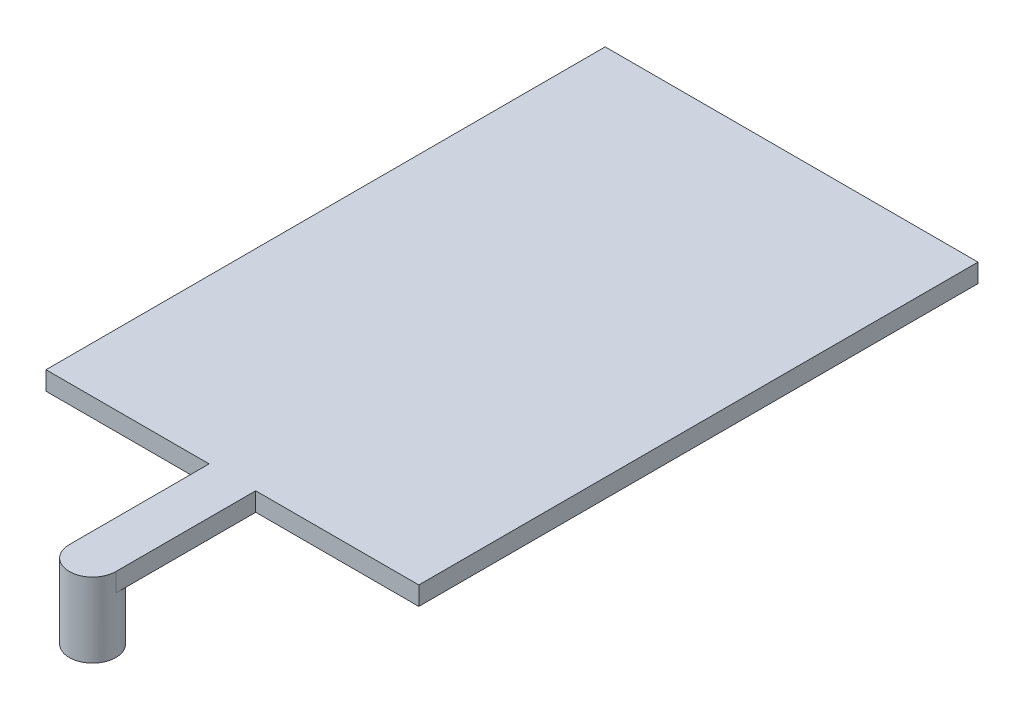
SolidWorks part; units mm, degrees
material "Медь"
ref_plane "Спереди" through (0, 0, 0) normal (0, 0, 1) x (1, 0, 0)
ref_plane "Сверху" through (0, 0, 0) normal (0, 1, 0) x (1, 0, 0)
ref_plane "Справа" through (0, 0, 0) normal (1, 0, 0) x (0, 0, -1)
sketch "Эскиз1" plane through (0, 0, 0) normal (0, 1, 0) x (1, 0, 0)
  line L0 (-0.125, -1.5) -> (0.125, -1.5)
  line L1 (-1, -1.5) -> (1, -1.5)
  line L2 (-1, -1.5) -> (-1, 1.5)
  line L3 (-1, 1.5) -> (1, 1.5)
  line L4 (1, -1.5) -> (1, 1.5)
  line L5 (-1, -1.5) -> (1, 1.5) construction
  line L6 (-1, 1.5) -> (1, -1.5) construction
  line L7 (-0.125, -1.5) -> (-0.125, -2.25)
  line L8 (0.125, -1.5) -> (0.125, -2.25)
  line L9 (-0.125, -2.25) -> (0.125, -2.25)
  point P0 (0, 0)
  dimension "D1" = 2
  dimension "D2" = 3
  dimension "D3" = 0.25
  dimension "D4" = 0.875
  dimension "D5" = 0.75
extrude "Бобышка-Вытянуть1" add sketch "Эскиз1" along normal blind 0.1 contours L1 L4 L3 L2 L0 | L7 L9 L8 L0
sketch "Эскиз2" plane through (0, 0.1, 0) normal (0, 1, 0) x (1, 0, 0)
  line L0 (-0.125, -2.25) -> (0.125, -2.25) construction
  circle A0 centre (0, -2.25) radius 0.125
extrude "Бобышка-Вытянуть2" add sketch "Эскиз2" against normal blind 0.4
